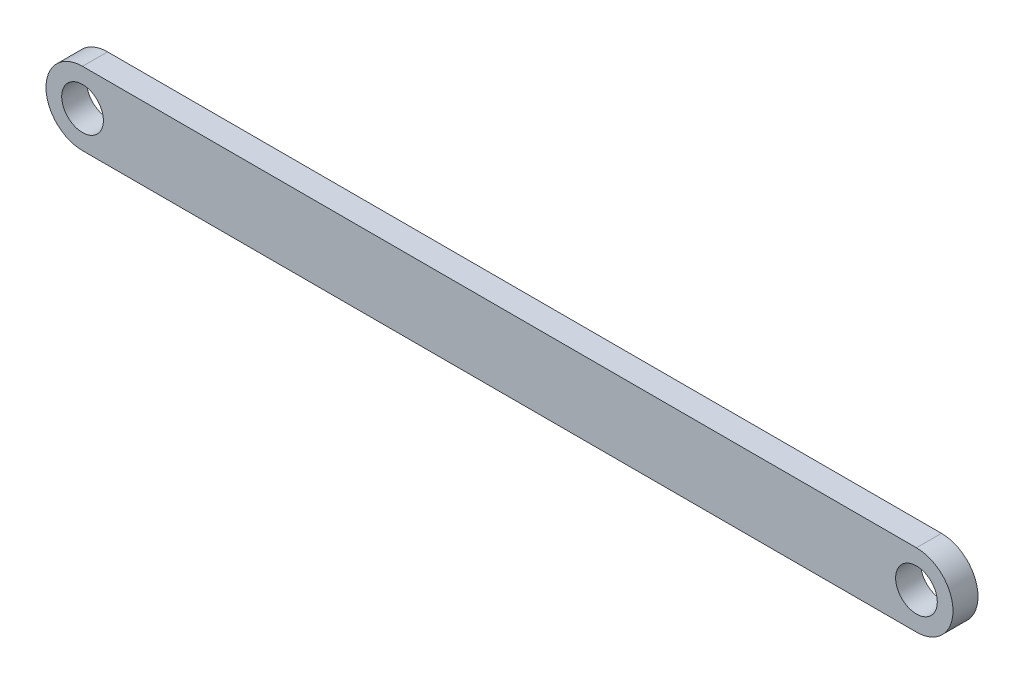
SolidWorks part; units mm, degrees
ref_plane "Alzado" through (0, 0, 0) normal (0, 0, 1) x (1, 0, 0)
ref_plane "Planta" through (0, 0, 0) normal (0, 1, 0) x (1, 0, 0)
ref_plane "Vista lateral" through (0, 0, 0) normal (1, 0, 0) x (0, 0, -1)
sketch "Croquis1" plane through (0, 0, 0) normal (0, 0, 1) x (1, 0, 0)
  line L0 (-32.6752, 0) -> (167.3248, 0) construction
  line L1 (-32.6752, 8.7631) -> (167.3248, 8.7631)
  line L2 (-32.6752, -8.7631) -> (167.3248, -8.7631)
  arc A0 (-32.6752, 8.7631) -> (-32.6752, -8.7631) centre (-32.6752, 0) ccw
  arc A1 (167.3248, -8.7631) -> (167.3248, 8.7631) centre (167.3248, 0) ccw
  circle A2 centre (-32.6752, 0) radius 5
  circle A3 centre (167.3248, 0) radius 5
  point P3 (67.3248, 0)
  dimension "D1" = 10
  dimension "D2" = 200
extrude "Saliente-Extruir1" add sketch "Croquis1" along normal blind 6
